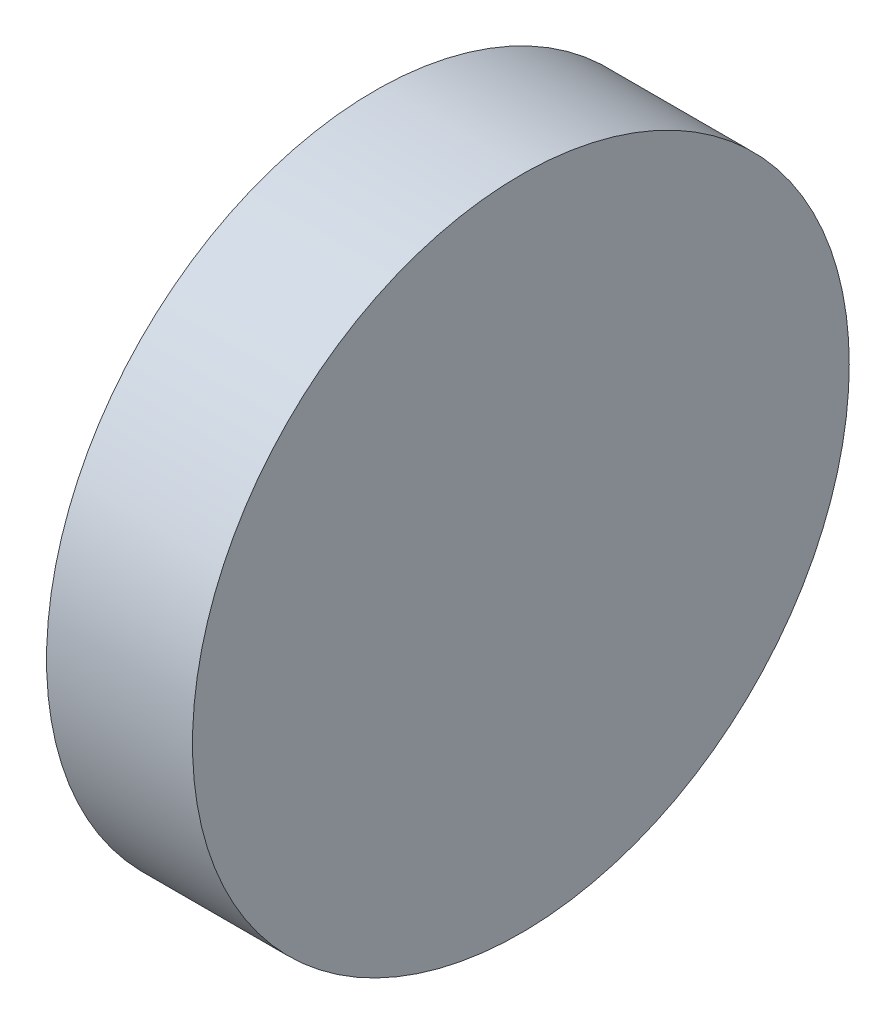
SolidWorks part; units mm, degrees
ref_plane "Plan de face" through (0, 0, 0) normal (0, 0, 1) x (1, 0, 0)
ref_plane "Plan de dessus" through (0, 0, 0) normal (0, 1, 0) x (1, 0, 0)
ref_plane "Plan de droite" through (0, 0, 0) normal (1, 0, 0) x (0, 0, -1)
sketch "Esquisse1" plane through (0, 0, 0) normal (1, 0, 0) x (0, 0, -1)
  circle A0 centre (0, 0) radius 22.5
  dimension "D1" = 45
extrude "Boss.-Extru.1" add sketch "Esquisse1" along normal blind 10
